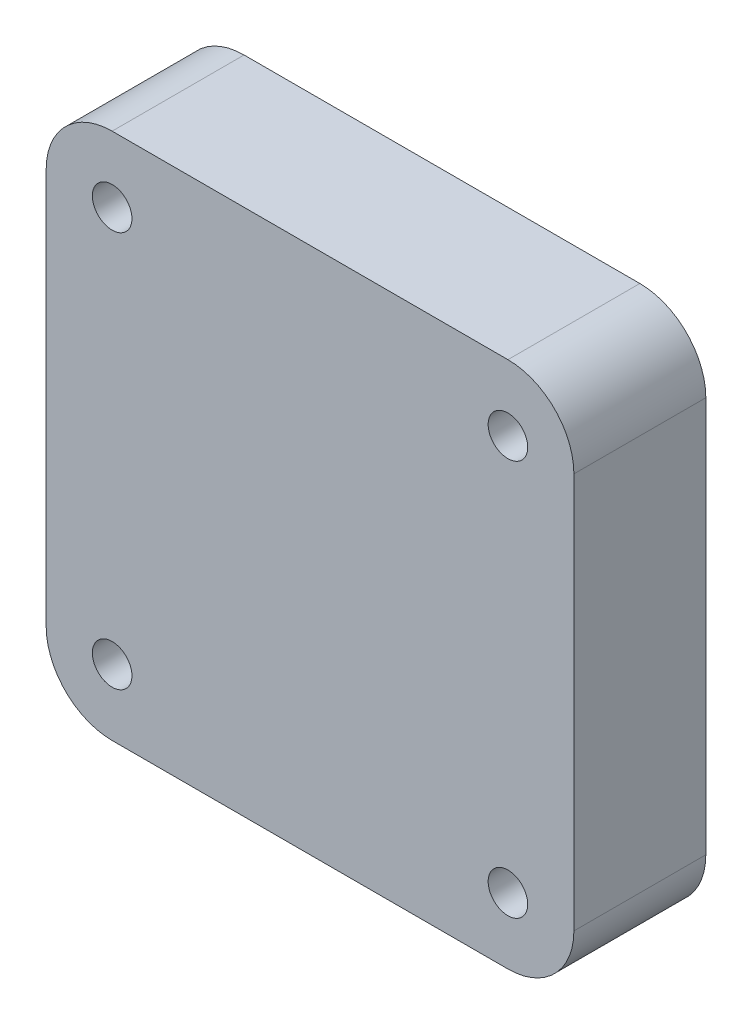
SolidWorks part; units mm, degrees
material "ABS"
ref_plane "前视基准面" through (0, 0, 0) normal (0, 0, 1) x (1, 0, 0)
ref_plane "上视基准面" through (0, 0, 0) normal (0, 1, 0) x (1, 0, 0)
ref_plane "右视基准面" through (0, 0, 0) normal (1, 0, 0) x (0, 0, -1)
other "Configuration Table"
sketch "草图1" plane through (0, 0, 0) normal (0, 0, 1) x (1, 0, 0)
  line L0 (-15, 15) -> (15, 15) construction
  line L1 (-20, 20) -> (20, 20)
  line L2 (-20, 20) -> (-20, -20)
  line L3 (-20, -20) -> (20, -20)
  line L4 (20, 20) -> (20, -20)
  line L5 (-20, 20) -> (20, -20) construction
  line L6 (-20, -20) -> (20, 20) construction
  line L7 (15, 15) -> (15, -15) construction
  line L8 (15, -15) -> (-15, -15) construction
  line L9 (-15, -15) -> (-15, 15) construction
  circle A0 centre (-15, 15) radius 1.5
  circle A1 centre (15, 15) radius 1.5
  circle A2 centre (-15, -15) radius 1.5
  circle A3 centre (15, -15) radius 1.5
  point P0 (0, 0)
  dimension "D4" = 3
  dimension "D1" = 40
  dimension "D2" = 40
  dimension "D3" = 30
extrude "凸台-拉伸1" add sketch "草图1" along normal blind 10
fillet "圆角1" radius 5 4 edges at (-20, -20, 5) (20, -20, 5) (20, 20, 5) (-20, 20, 5)
